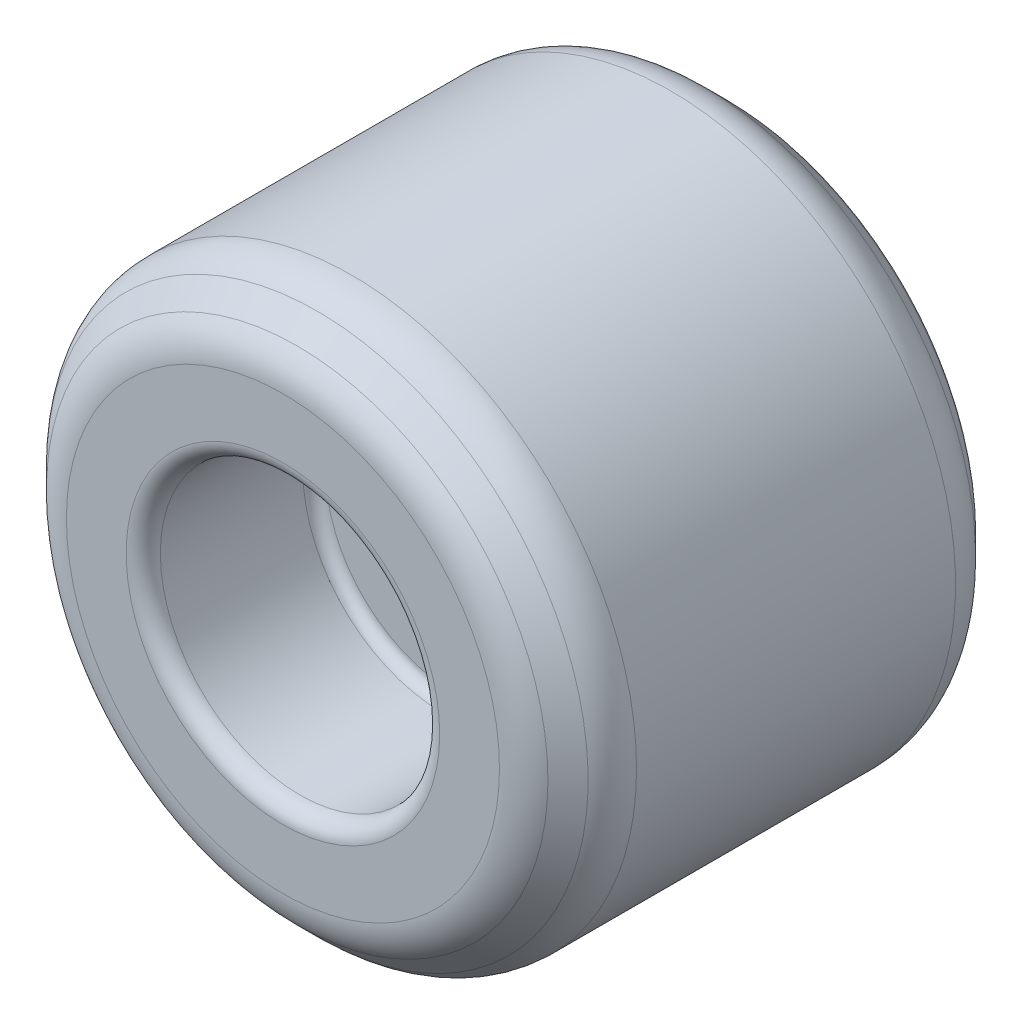
SolidWorks part; units mm, degrees
ref_plane "Front Plane" through (0, 0, 0) normal (0, 0, 1) x (1, 0, 0)
ref_plane "Top Plane" through (0, 0, 0) normal (0, 1, 0) x (1, 0, 0)
ref_plane "Right Plane" through (0, 0, 0) normal (1, 0, 0) x (0, 0, -1)
sketch "Sketch1" plane through (0, 0, 0) normal (0, 0, 1) x (1, 0, 0)
  circle A0 centre (0, 0) radius 6.35
  dimension "D1" = 12.7
extrude "Boss-Extrude1" add sketch "Sketch1" along normal blind 10.16
sketch "Sketch2" plane through (0, 0, 10.16) normal (0, 0, 1) x (1, 0, 0)
  circle A0 centre (0, 0) radius 3.1115
  dimension "D1" = 6.223
extrude "Cut-Extrude1" cut sketch "Sketch2" against normal blind 3.81
ref_plane "Plane1" through (0, 0, 5.08) normal (0, 0, 1) x (1, 0, 0)
mirror "Mirror1" about plane through (0, 0, 5.08) normal (0, 0, 1) of "Cut-Extrude1"
chamfer "Chamfer1" distance 1.0795 angle 45 2 edges at (6.35, 0, 0) (6.35, 0, 10.16)
fillet "Fillet1" radius 0.254 2 edges at (3.1115, 0, 6.35) (3.1115, 0, 3.81)
fillet "Fillet2" radius 0.381 2 edges at (3.1115, 0, 0) (3.1115, 0, 10.16)
fillet "Fillet3" radius 1.0795 4 edges at (5.2705, 0, 10.16) (6.35, 0, 9.0805) (6.35, 0, 1.0795) (5.2705, 0, 0)
